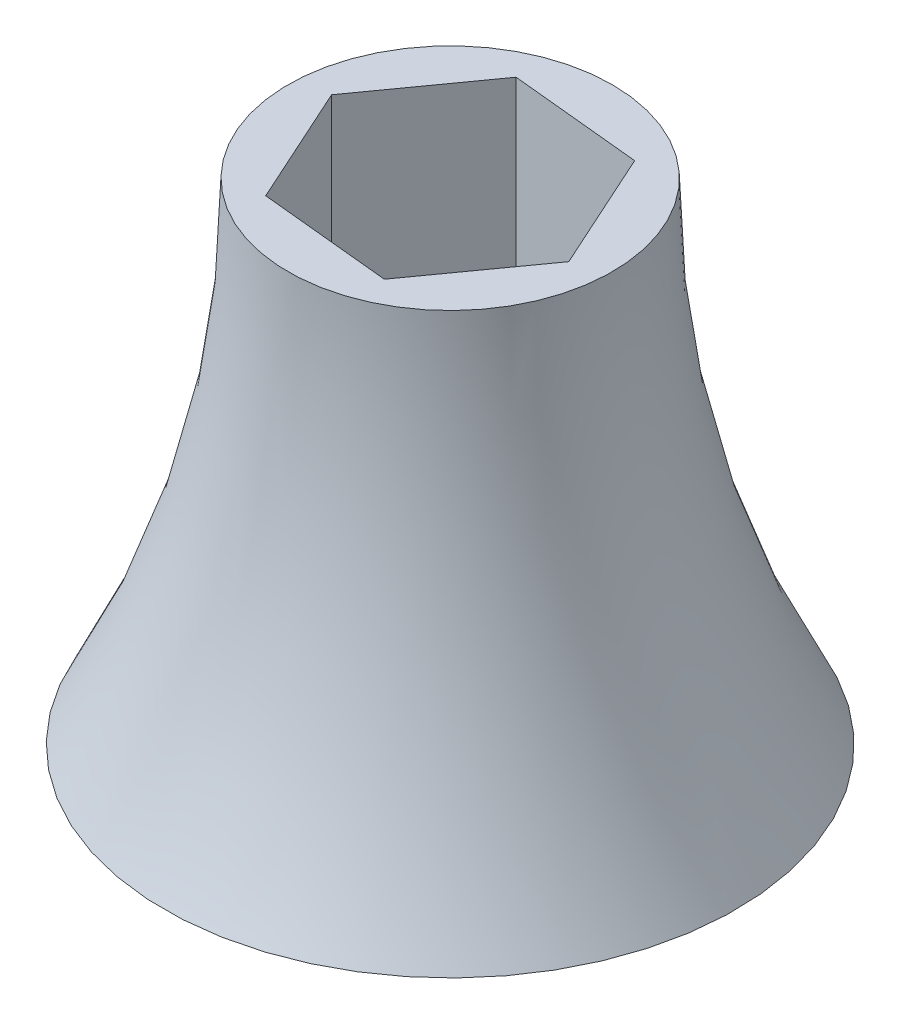
SolidWorks part; units mm, degrees
ref_plane "Front Plane" through (0, 0, 0) normal (0, 0, 1) x (1, 0, 0)
ref_plane "Top Plane" through (0, 0, 0) normal (0, 1, 0) x (1, 0, 0)
ref_plane "Right Plane" through (0, 0, 0) normal (1, 0, 0) x (0, 0, -1)
sketch "Sketch1" plane through (0, 0, 0) normal (0, 1, 0) x (1, 0, 0)
  circle A0 centre (0, 0) radius 33.274
  point P3 (0, 0)
  point P4 (0, 0)
extrude "Boss-Extrude1" add sketch "Sketch1" along normal blind 57.15
sketch "Sketch2" plane through (0, 0, 0) normal (0, -1, 0) x (1, 0, 0)
  line L1 (-15.3236, -1.5108) -> (-6.3534, -14.026)
  line L2 (-6.3534, -14.026) -> (8.9702, -12.5153)
  line L3 (8.9702, -12.5153) -> (15.3236, 1.5108)
  line L4 (15.3236, 1.5108) -> (6.3534, 14.026)
  line L5 (6.3534, 14.026) -> (-8.9702, 12.5153)
  line L6 (-8.9702, 12.5153) -> (-15.3236, -1.5108)
  circle A0 centre (0, 0) radius 13.335 construction
  point P1 (0, 0)
  dimension "D1" = 26.67
extrude "Cut-Extrude1" cut sketch "Sketch2" against normal up to surface (57.15 mm away) up to face at (0, 57.15, 33.274)
sketch "Sketch4" plane through (0, 0, 0) normal (0, 0, 1) x (1, 0, 0)
  line L1 (0, 0) -> (0, 57.15) construction
  line L2 (33.274, 57.15) -> (-33.274, 57.15) construction
  line L3 (-33.274, 57.15) -> (-33.274, 114.3) construction
  circle A2 centre (-139.5298, 57.15) radius 120.65
  point P2 (0, 0)
  dimension "D1" = 57.15
  dimension "D2" = 57.15
sketch "Sketch5" plane through (0, 0, 0) normal (0, 0, 1) x (1, 0, 0)
  line L1 (-39.6693, 52.3875) -> (39.39, 52.3875)
  line L2 (-39.6693, 52.3875) -> (-39.6693, 0)
  line L3 (-39.6693, 0) -> (39.39, 0)
  line L4 (39.39, 52.3875) -> (39.39, 0)
revolve "Cut-Revolve2" cut sketch "Sketch4" angle 360 about L1
